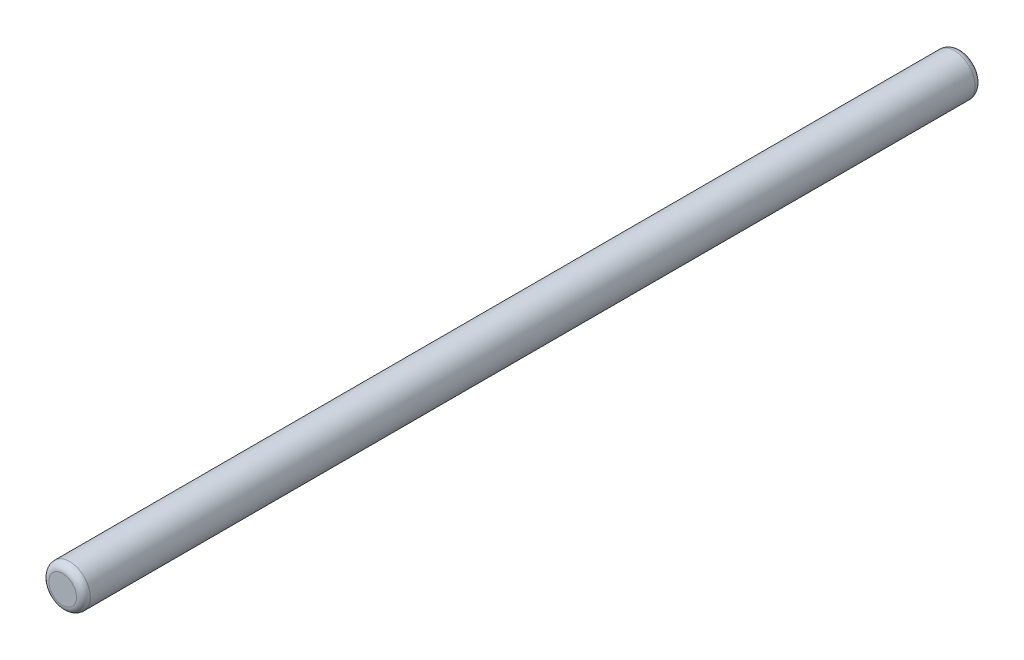
SolidWorks part; units mm, degrees
ref_plane "Piano frontale" through (0, 0, 0) normal (0, 0, 1) x (1, 0, 0)
ref_plane "Piano superiore" through (0, 0, 0) normal (0, 1, 0) x (1, 0, 0)
ref_plane "Piano destro" through (0, 0, 0) normal (1, 0, 0) x (0, 0, -1)
sketch "Schizzo1" plane through (0, 0, 0) normal (0, 0, 1) x (1, 0, 0)
  circle A0 centre (0, 0) radius 1.5
  dimension "D1" = 3
extrude "Estrusione-Estrusione1" add sketch "Schizzo1" along normal blind 65
fillet "Raccordo1" radius 0.5 2 edges at (1.5, 0, 0) (1.5, 0, 65)
